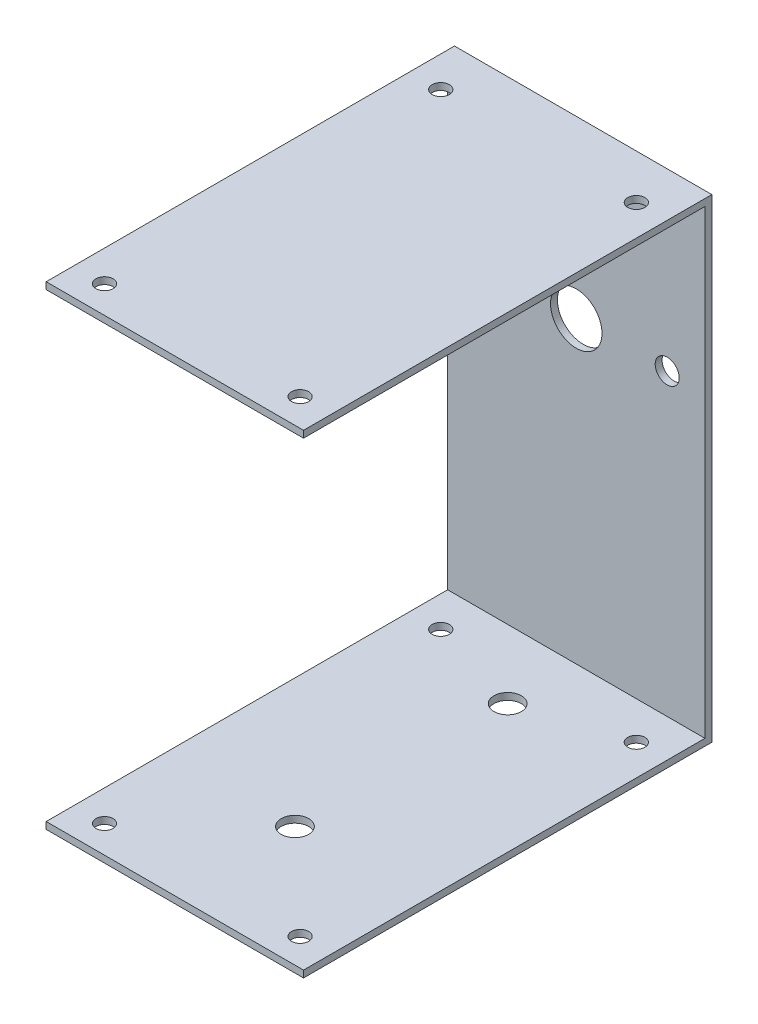
SolidWorks part; units mm, degrees
material "Liga 1060"
ref_plane "Plano frontal" through (0, 0, 0) normal (0, 0, 1) x (1, 0, 0)
ref_plane "Plano superior" through (0, 0, 0) normal (0, 1, 0) x (1, 0, 0)
ref_plane "Plano direito" through (0, 0, 0) normal (1, 0, 0) x (0, 0, -1)
sketch "Esboço1" plane through (0, 0, 0) normal (0, 1, 0) x (1, 0, 0)
  line L1 (-37.5, 58.5) -> (37.5, 58.5)
  line L2 (-37.5, 58.5) -> (-37.5, -58.5)
  line L3 (-37.5, -58.5) -> (37.5, -58.5)
  line L4 (37.5, 58.5) -> (37.5, -58.5)
  line L5 (-37.5, 58.5) -> (37.5, -58.5) construction
  line L6 (-37.5, -58.5) -> (37.5, 58.5) construction
  point P0 (0, 0)
  dimension "D1" = 75
  dimension "D2" = 117
extrude "Ressalto-extrusão1" add sketch "Esboço1" along normal blind 2
sketch "Esboço2" plane through (0, 0, 0) normal (0, 1, 0) x (1, 0, 0)
  line L0 (37.5, -58.5) -> (37.5, 58.5) construction
  line L1 (-37.5, 58.5) -> (37.5, 58.5)
  line L2 (-37.5, 58.5) -> (-37.5, 60.5)
  line L3 (-37.5, 60.5) -> (37.5, 60.5)
  line L4 (37.5, 58.5) -> (37.5, 60.5)
  dimension "D1" = 2
extrude "Ressalto-extrusão2" add sketch "Esboço2" along normal blind 136.25
sketch "Esboço3" plane through (0, 136.25, 0) normal (0, 1, 0) x (1, 0, 0)
  line L4 (37.5, -58.5) -> (37.5, 60.5)
  line L5 (-37.5, -58.5) -> (37.5, -58.5)
  line L6 (-37.5, 60.5) -> (-37.5, -58.5)
  line L7 (37.5, 60.5) -> (-37.5, 60.5)
  line L8 (37.5, -58.5) -> (37.5, 60.5)
  line L9 (-37.5, -58.5) -> (37.5, -58.5)
  line L10 (-37.5, 60.5) -> (-37.5, -58.5)
  line L11 (37.5, 60.5) -> (-37.5, 60.5)
  dimension "D1" = 0
extrude "Ressalto-extrusão3" add sketch "Esboço3" along normal blind 2
sketch "Esboço4" plane through (0, 0, 0) normal (0, -1, 0) x (1, 0, 0)
  line L0 (37.5, -60.5) -> (-37.5, -60.5) construction
  line L1 (37.5, 58.5) -> (37.5, -60.5) construction
  line L2 (-37.5, -60.5) -> (-37.5, 58.5) construction
  line L3 (-37.5, 58.5) -> (37.5, 58.5) construction
  circle A0 centre (28.5, -47.5) radius 2.5
  circle A1 centre (-28.5, -47.5) radius 2.5
  circle A2 centre (28.5, 50.5) radius 2.5
  circle A3 centre (-28.5, 50.5) radius 2.5
  dimension "D1" = 5
  dimension "D4" = 5
  dimension "D9" = 5
  dimension "D10" = 5
  dimension "D11" = 9
  dimension "D2" = 13
  dimension "D3" = 9
  dimension "D5" = 9
  dimension "D6" = 13
  dimension "D7" = 8
  dimension "D8" = 9
  dimension "D12" = 8
extrude "Corte-extrusão1" cut sketch "Esboço4" against normal through all
sketch "Esboço5" plane through (0, 0, -60.5) normal (0, 0, -1) x (-1, 0, 0)
  line L1 (-37.5, 138.25) -> (-37.5, 0) construction
  line L2 (-37.5, 0) -> (37.5, 0) construction
  circle A0 centre (0, 35.2) radius 3.5
  circle A1 centre (0, 89.2) radius 7.5
  dimension "D1" = 7
  dimension "D4" = 15
  dimension "D2" = 37.5
  dimension "D3" = 35.2
  dimension "D5" = 54
extrude "Corte-extrusão2" cut sketch "Esboço5" against normal blind 10 contours A1
sketch "Esboço6" plane through (0, 0, -58.5) normal (0, 0, 1) x (1, 0, 0)
  arc A0 (26.5, 85.7) -> (26.5, 92.7) centre (26.5, 89.2) ccw construction
  arc A1 (26.5, 92.7) -> (26.5, 85.7) centre (26.5, 89.2) ccw construction
  arc A2 (-26.5, 85.7) -> (-26.5, 92.7) centre (-26.5, 89.2) ccw construction
  arc A3 (-26.5, 92.7) -> (-26.5, 85.7) centre (-26.5, 89.2) ccw construction
  arc A4 (26.5, 85.7) -> (26.5, 92.7) centre (26.5, 89.2) ccw
  arc A5 (26.5, 92.7) -> (26.5, 85.7) centre (26.5, 89.2) ccw
  arc A6 (-26.5, 85.7) -> (-26.5, 92.7) centre (-26.5, 89.2) ccw
  arc A7 (-26.5, 92.7) -> (-26.5, 85.7) centre (-26.5, 89.2) ccw
extrude "Corte-extrusão3" cut sketch "Esboço6" against normal blind 10
sketch "Esboço7" plane through (0, 0, 0) normal (0, -1, 0) x (1, 0, 0)
  line L0 (0, -60.5) -> (0, 58.5) construction
  line L1 (37.5, -60.5) -> (-37.5, -60.5) construction
  line L2 (-37.5, 58.5) -> (37.5, 58.5) construction
  circle A0 centre (0, -38.5) radius 4
  circle A1 centre (0, 23.5) radius 4
  dimension "D1" = 8
  dimension "D2" = 8
  dimension "D3" = 22
  dimension "D4" = 35
extrude "Corte-extrusão4" cut sketch "Esboço7" against normal blind 10
